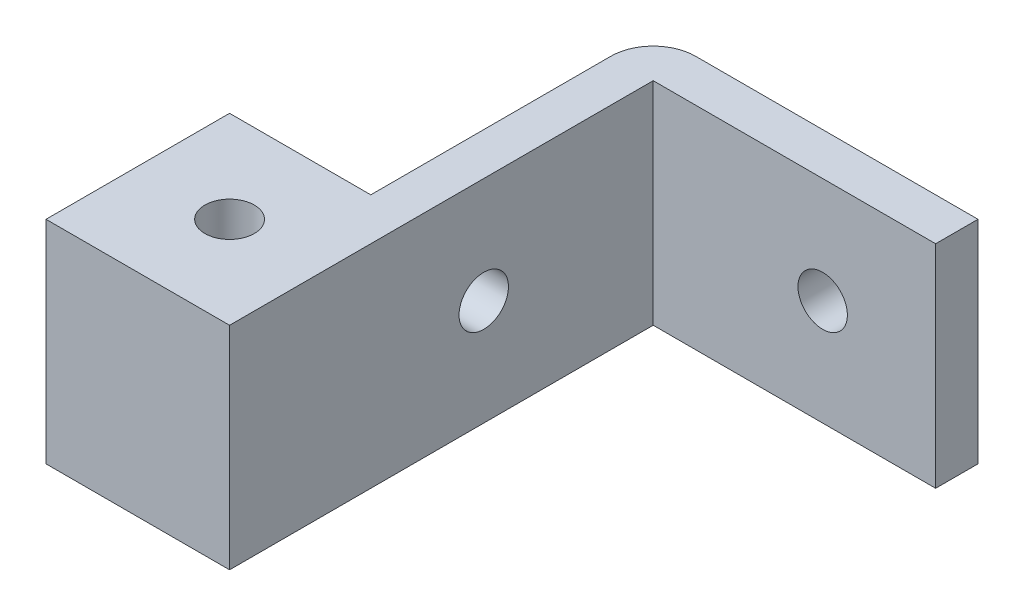
SolidWorks part; units mm, degrees
ref_plane "Front Plane" through (0, 0, 0) normal (0, 0, 1) x (1, 0, 0)
ref_plane "Top Plane" through (0, 0, 0) normal (0, 1, 0) x (1, 0, 0)
ref_plane "Right Plane" through (0, 0, 0) normal (1, 0, 0) x (0, 0, -1)
sketch "Sketch1" plane through (0, 0, 0) normal (0, 0, 1) x (1, 0, 0)
  line L1 (-11.5, -7.5) -> (11.5, -7.5)
  line L2 (-11.5, -7.5) -> (-11.5, 7.5)
  line L3 (-11.5, 7.5) -> (11.5, 7.5)
  line L4 (11.5, -7.5) -> (11.5, 7.5)
  line L5 (-11.5, -7.5) -> (11.5, 7.5) construction
  line L6 (-11.5, 7.5) -> (11.5, -7.5) construction
  point P0 (0, 0)
  dimension "D1" = 23
  dimension "D2" = 15
extrude "Boss-Extrude1" add sketch "Sketch1" along normal blind 3
sketch "Sketch10" plane through (0, 0, 3) normal (0, 0, 1) x (1, 0, 0)
  line L0 (-11.5, -7.5) -> (11.5, -7.5) construction
  line L1 (-11.5, 7.5) -> (-8.5, 7.5)
  line L2 (-11.5, 7.5) -> (-11.5, -7.5)
  line L3 (-11.5, -7.5) -> (-8.5, -7.5)
  line L4 (-8.5, 7.5) -> (-8.5, -7.5)
  dimension "D1" = 3
extrude "Boss-Extrude2" add sketch "Sketch10" along normal blind 20
sketch "Sketch13" plane through (0, 0, 0) normal (0, 0, -1) x (-1, 0, 0)
  line L0 (11.5, 7.5) -> (11.5, -7.5) construction
  circle A0 centre (-3.5, 0) radius 1.75
  dimension "D1" = 3.5
  dimension "D2" = 15
extrude "Cut-Extrude3" cut sketch "Sketch13" against normal through all
sketch "Sketch14" plane through (-11.5, 0, 0) normal (-1, 0, 0) x (0, 0, 1)
  circle A0 centre (15, 0) radius 1.75
  dimension "D1" = 3.5
  dimension "D2" = 15
extrude "Cut-Extrude4" cut sketch "Sketch14" against normal through all
fillet "Fillet1" radius 3 1 edges at (-11.5, 0, 0)
sketch "Sketch15" plane through (0, 0, 23) normal (0, 0, 1) x (1, 0, 0)
  line L0 (-11.5, 7.5) -> (-11.5, -7.5) construction
  line L1 (-11.5, -7.5) -> (-8.5, -7.5)
  line L2 (-11.5, -7.5) -> (-11.5, 7.5)
  line L3 (-11.5, 7.5) -> (-8.5, 7.5)
  line L4 (-8.5, -7.5) -> (-8.5, 7.5)
  line L5 (-8.5, -7.5) -> (-8.5, 7.5) construction
  line L6 (-8.5, 7.5) -> (-11.5, 7.5) construction
  line L8 (-11.5, -7.5) -> (-8.5, -7.5) construction
extrude "Boss-Extrude3" add sketch "Sketch15" along normal blind 10
sketch "Sketch16" plane through (-11.5, 0, 0) normal (-1, 0, 0) x (0, 0, 1)
  line L0 (33, -7.5) -> (3, -7.5) construction
  line L1 (33, -7.5) -> (20, -7.5)
  line L2 (33, -7.5) -> (33, 7.5)
  line L3 (33, 7.5) -> (20, 7.5)
  line L4 (20, -7.5) -> (20, 7.5)
  line L5 (33, 7.5) -> (3, 7.5) construction
  line L6 (33, 7.5) -> (33, -7.5) construction
  dimension "D1" = 13
extrude "Boss-Extrude4" add sketch "Sketch16" along normal blind 10
sketch "Sketch17" plane through (0, -7.5, 0) normal (0, -1, 0) x (1, 0, 0)
  line L0 (-21.5, 20) -> (-21.5, 33) construction
  line L1 (-21.5, 33) -> (-8.5, 33) construction
  circle A0 centre (-15, 26.5) radius 1.75
  point P4 (-21.5, 26.5)
  point P5 (0, 0)
  point P6 (-16.4318, 24.1151)
  point P9 (-15, 33)
  dimension "D1" = 3.5
extrude "Cut-Extrude5" cut sketch "Sketch17" against normal through all
sketch "Bend-Lines1" plane through (0, 0, 0) normal (0, 1, 0) x (1, 0, 0)
sketch "Bounding-Box1" plane through (0, 0, 0) normal (0, 1, 0) x (1, 0, 0)
